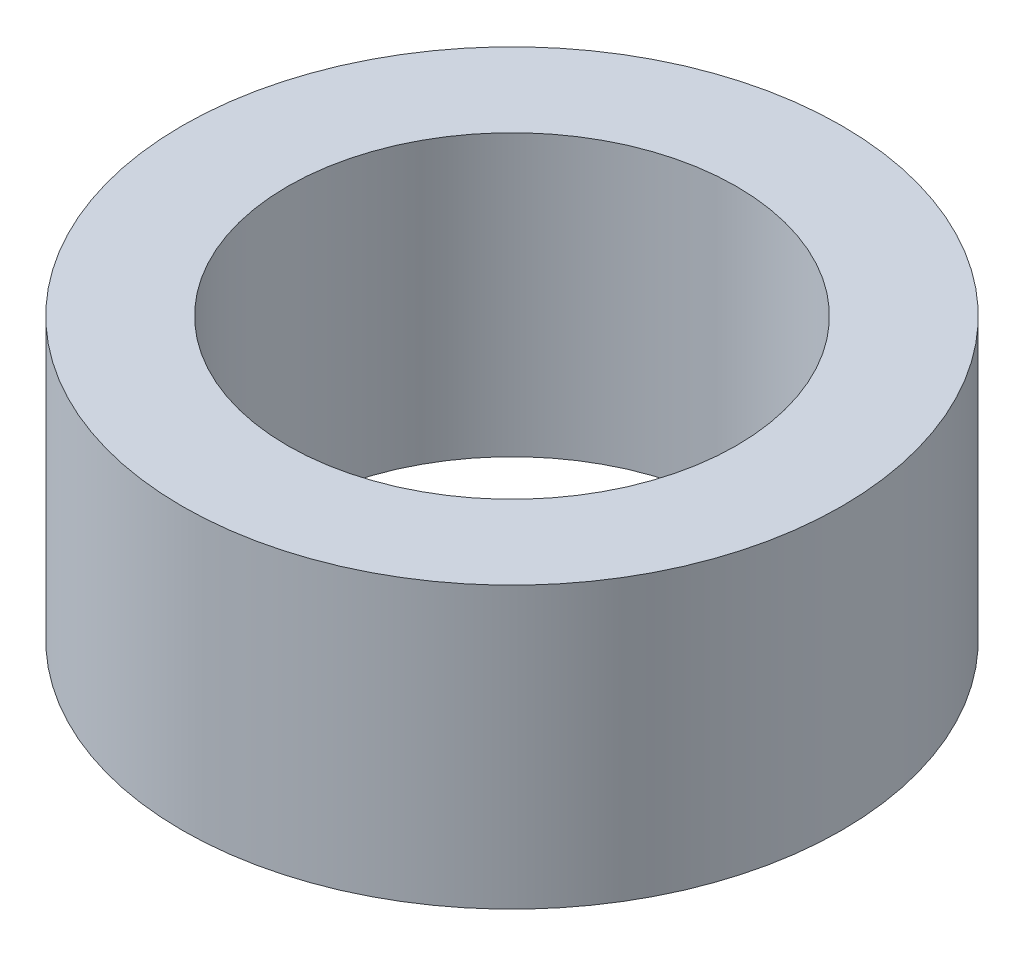
SolidWorks part; units mm, degrees
ref_plane "Front Plane" through (0, 0, 0) normal (0, 0, 1) x (1, 0, 0)
ref_plane "Top Plane" through (0, 0, 0) normal (0, 1, 0) x (1, 0, 0)
ref_plane "Right Plane" through (0, 0, 0) normal (1, 0, 0) x (0, 0, -1)
sketch "Sketch1" plane through (0, 0, 0) normal (0, 1, 0) x (1, 0, 0)
  circle A0 centre (0, 0) radius 1.6
  circle A1 centre (0, 0) radius 2.35
  dimension "D1" = 3.2
  dimension "D2" = 4.7
extrude "Boss-Extrude1" add sketch "Sketch1" along normal blind 2
